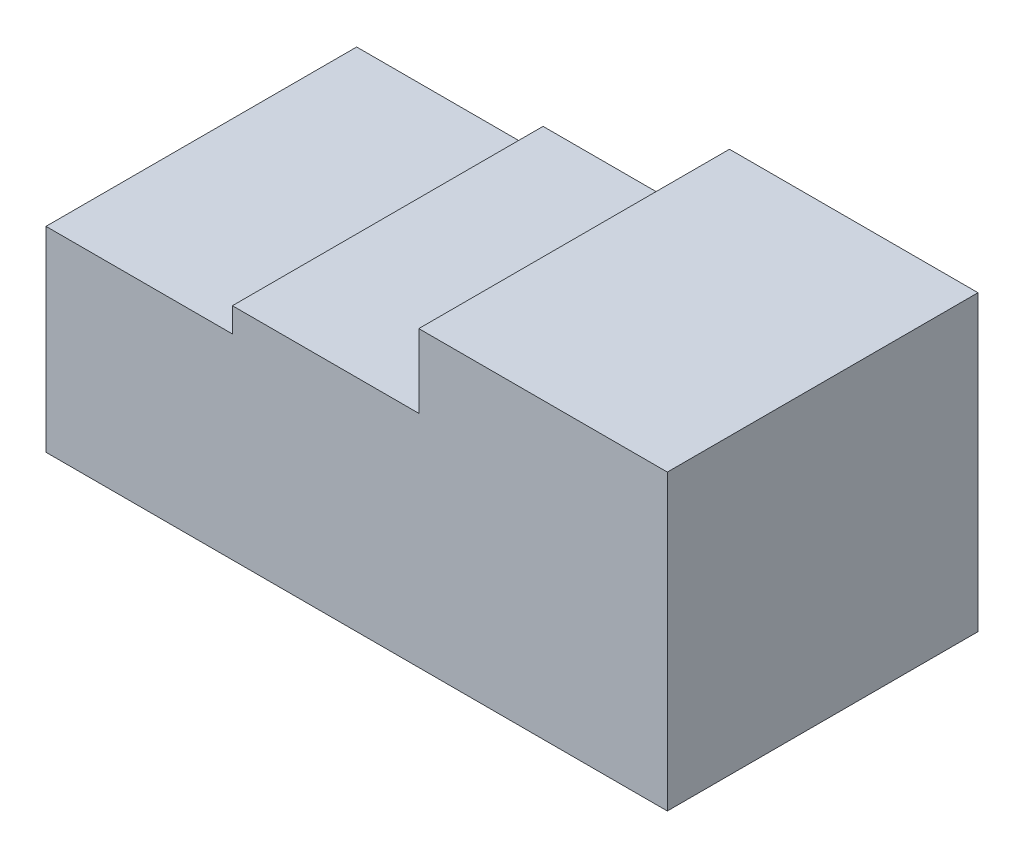
SolidWorks part; units mm, degrees
ref_plane "Front Plane" through (0, 0, 0) normal (0, 0, 1) x (1, 0, 0)
ref_plane "Top Plane" through (0, 0, 0) normal (0, 1, 0) x (1, 0, 0)
ref_plane "Right Plane" through (0, 0, 0) normal (1, 0, 0) x (0, 0, -1)
sketch "Sketch1" plane through (0, 0, 0) normal (0, 0, 1) x (1, 0, 0)
  line L0 (0, 0) -> (50.8, 0)
  line L1 (0, 0) -> (0, 16) construction
  line L2 (0, 14) -> (50.8, 14) construction
  line L3 (0, 16) -> (15.24, 16)
  line L4 (15.24, 16) -> (15.24, 18)
  line L5 (15.24, 18) -> (30.48, 18)
  line L6 (30.48, 18) -> (30.48, 24)
  line L7 (30.48, 24) -> (50.8, 24)
  line L8 (50.8, 0) -> (50.8, 24)
  line L9 (0, 0) -> (0, 16)
  point P3 (0, 14)
  dimension "D1" = 50.8
  dimension "D2" = 16
  dimension "D3" = 14
  dimension "D4" = 50.8
  dimension "D5" = 15.24
  dimension "D6" = 2
  dimension "D7" = 15.24
  dimension "D8" = 6
extrude "Boss-Extrude1" add sketch "Sketch1" along normal blind 25.4
sketch "Sketch2" plane through (0, 0, 0) normal (0, 0, -1) x (-1, 0, 0)
  text T0 "2 mm" font "Century Gothic" height in points 10
  text T1 "4 mm" font "Century Gothic" height in points 10
  text T2 "10 mm" font "Century Gothic" height in points 10
  point P1 (-11.9245, 9.2273)
  point P2 (-13.4217, 9.0609)
  point P3 (0, 0)
  point P5 (-24.5127, 11.7782)
  point P6 (-25.6773, 12.3882)
  point P7 (-27.6182, 11.8891)
  point P9 (-46.1401, 18.1555)
  point P10 (0, 0)
extrude "Cut-Extrude1" cut sketch "Sketch2" against normal blind 4
